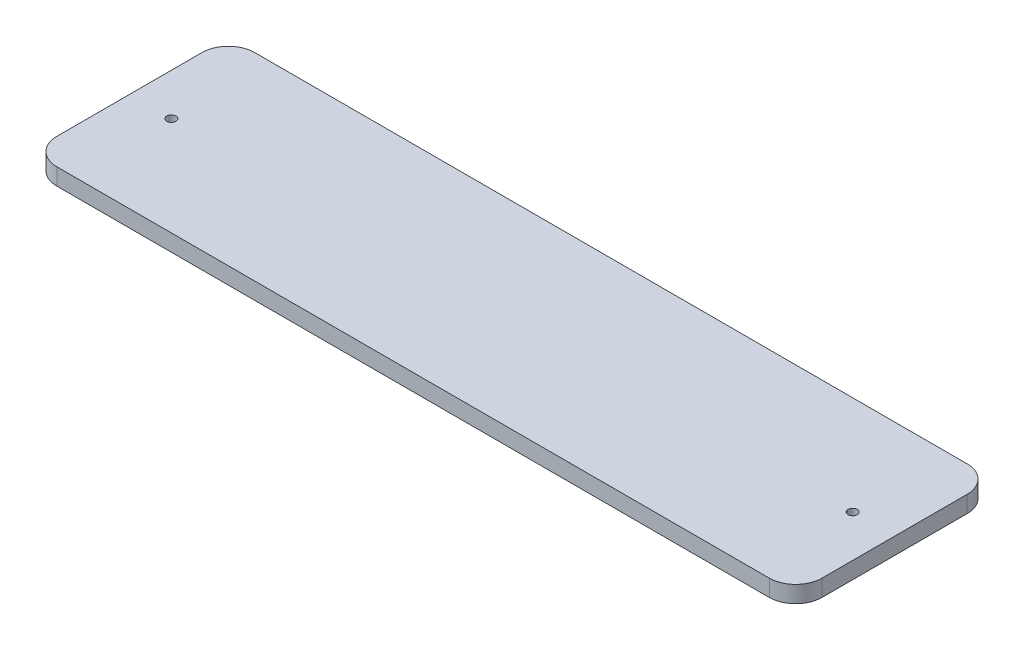
SolidWorks part; units mm, degrees
ref_plane "Front Plane" through (0, 0, 0) normal (0, 0, 1) x (1, 0, 0)
ref_plane "Top Plane" through (0, 0, 0) normal (0, 1, 0) x (1, 0, 0)
ref_plane "Right Plane" through (0, 0, 0) normal (1, 0, 0) x (0, 0, -1)
sketch "Sketch1" plane through (0, 0, 0) normal (0, 1, 0) x (1, 0, 0)
  line L1 (-145, 37.5) -> (145, 37.5)
  line L2 (-145, 37.5) -> (-145, -37.5)
  line L3 (-145, -37.5) -> (145, -37.5)
  line L4 (145, 37.5) -> (145, -37.5)
  line L5 (-145, 37.5) -> (145, -37.5) construction
  line L6 (-145, -37.5) -> (145, 37.5) construction
  point P0 (0, 0)
  dimension "D1" = 290
  dimension "D2" = 75
extrude "Boss-Extrude1" add sketch "Sketch1" along normal blind 6.35
sketch "Sketch2" plane through (0, 6.35, 0) normal (0, 1, 0) x (1, 0, 0)
  line L0 (145, 37.5) -> (-145, 37.5) construction
  circle A0 centre (-129.12, 0) radius 1.75
  dimension "D1" = 129.12
  dimension "D3" = 3.5
  dimension "D2" = 37.5
extrude "Cut-Extrude1" cut sketch "Sketch2" against normal through all
sketch "Sketch3" plane through (0, 6.35, 0) normal (0, 1, 0) x (1, 0, 0)
  line L1 (145, 37.5) -> (-145, 37.5) construction
  circle A0 centre (129.12, 0) radius 1.75
  dimension "D1" = 129.12
  dimension "D3" = 3.5
  dimension "D2" = 37.5
extrude "Cut-Extrude2" cut sketch "Sketch3" against normal through all
fillet "Fillet1" radius 10 4 edges at (145, 3.175, -37.5) (145, 3.175, 37.5) (-145, 3.175, 37.5) (-145, 3.175, -37.5)
